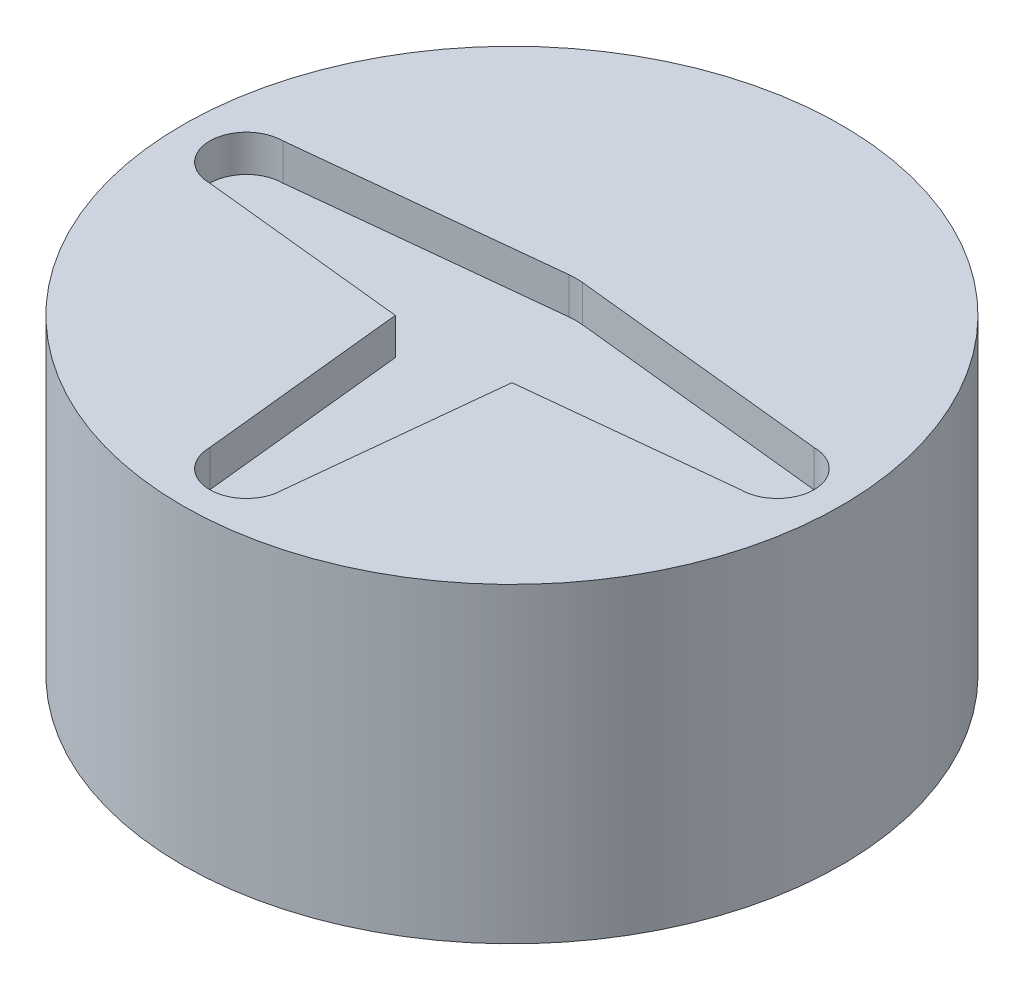
SolidWorks part; units mm, degrees
ref_plane "Front Plane" through (0, 0, 0) normal (0, 0, 1) x (1, 0, 0)
ref_plane "Top Plane" through (0, 0, 0) normal (0, 1, 0) x (1, 0, 0)
ref_plane "Right Plane" through (0, 0, 0) normal (1, 0, 0) x (0, 0, -1)
sketch "Sketch1" plane through (0, 0, 0) normal (0, 1, 0) x (1, 0, 0)
  circle A0 centre (0, 0) radius 18
extrude "Boss-Extrude1" add sketch "Sketch1" along normal blind 17
sketch "Sketch2" plane through (0, 0, 0) normal (0, -1, 0) x (1, 0, 0)
  line L1 (-13, 7) -> (13, 7)
  line L2 (-13, 7) -> (-13, -7)
  line L3 (-13, -7) -> (13, -7)
  line L4 (13, 7) -> (13, -7)
  line L5 (-13, 7) -> (13, -7) construction
  line L6 (-13, -7) -> (13, 7) construction
  point P0 (0, 0)
  dimension "D1" = 26
  dimension "D2" = 14
extrude "Cut-Extrude1" cut sketch "Sketch2" against normal blind 5.25 contours L2 L1 L4 L3
sketch "Sketch3" plane through (0, 17, 0) normal (0, 1, 0) x (1, 0, 0)
  line L0 (14.5, 2) -> (0.3647, 3.4809)
  line L1 (14.5, -2) -> (3.1854, -3.1854)
  line L2 (2, -14.5) -> (3.1854, -3.1854)
  line L3 (-2, -14.5) -> (-3.1854, -3.1854)
  line L4 (-14.5, -2) -> (-3.1854, -3.1854)
  line L5 (-14.5, 2) -> (-0.3647, 3.4809)
  arc A0 (14.5, -2) -> (14.5, 2) centre (14.5, 0) ccw
  arc A1 (-2, -14.5) -> (2, -14.5) centre (0, -14.5) ccw
  arc A2 (-14.5, 2) -> (-14.5, -2) centre (-14.5, 0) ccw
  arc A3 (0.3647, 3.4809) -> (-0.3647, 3.4809) centre (0, 0) ccw
extrude "Cut-Extrude2" cut sketch "Sketch3" against normal blind 2
